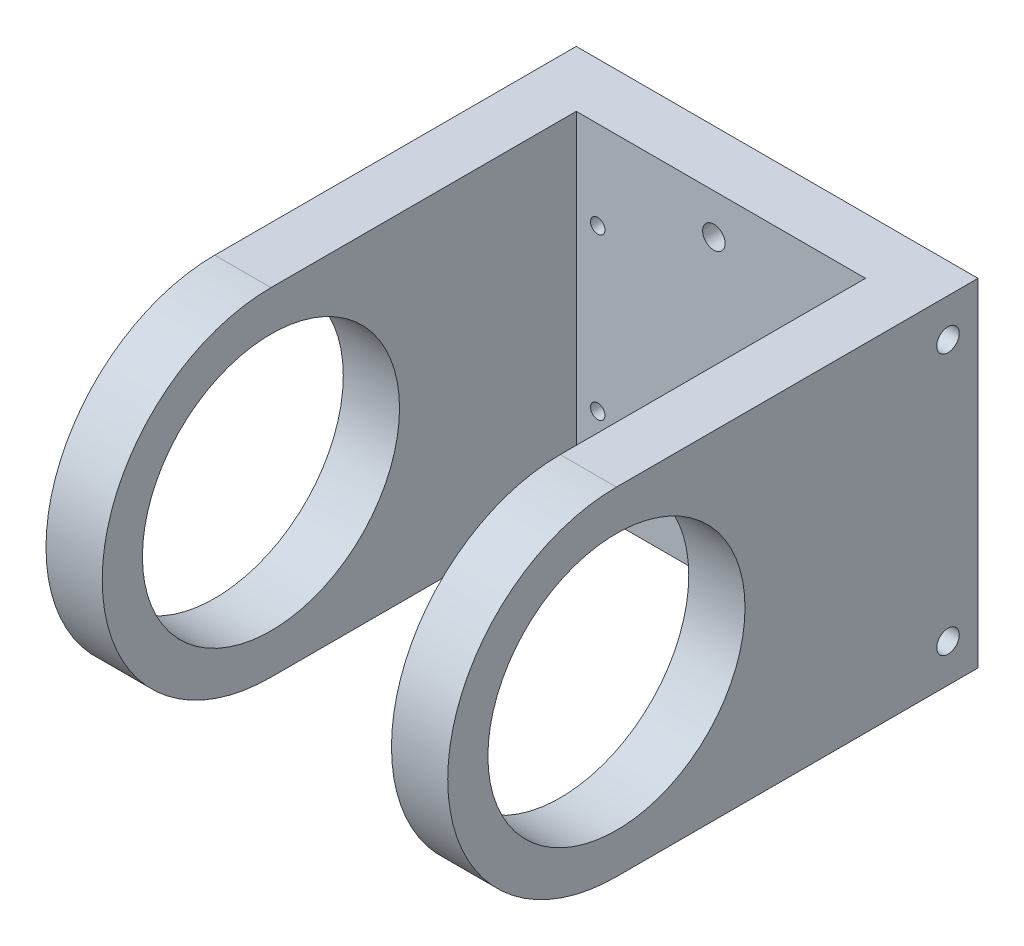
SolidWorks part; units mm, degrees
ref_plane "정면" through (0, 0, 0) normal (0, 0, 1) x (1, 0, 0)
ref_plane "윗면" through (0, 0, 0) normal (0, 1, 0) x (1, 0, 0)
ref_plane "우측면" through (0, 0, 0) normal (1, 0, 0) x (0, 0, -1)
ref_plane "평면1" through (-75, 0, 0) normal (-1, 0, 0) x (0, -1, 0)
sketch "스케치1" plane through (-75, 0, 0) normal (-1, 0, 0) x (0, -1, 0)
  line L0 (-21, 0) -> (-21, -45)
  line L1 (-21, -45) -> (21, -45)
  line L2 (21, -45) -> (21, 0)
  arc A0 (21, 0) -> (-21, 0) centre (0, 0) ccw
  dimension "D1" = 21
  dimension "D2" = 45
extrude "보스-돌출1" add sketch "스케치1" against normal blind 50
sketch "스케치2" plane through (0, 21, 0) normal (0, 1, 0) x (-1, 0, 0)
  line L0 (68, 64.1639) -> (32, 64.1639)
  line L1 (32, 64.1639) -> (32, -38)
  line L2 (32, -38) -> (68, -38)
  line L3 (68, -38) -> (68, 64.1639)
  line L4 (75, 0) -> (75, -45) construction
  line L5 (25, -45) -> (75, -45) construction
  line L6 (25, 0) -> (75, 0) construction
  circle A0 centre (50, 0) radius 21 construction
  dimension "D1" = 36
  dimension "D2" = 7
  dimension "D3" = 7
extrude "컷-돌출1" cut sketch "스케치2" against normal through all
hole_wizard "Ø1.8 (1.8) 지름 구멍1" positions "스케치4" profile "스케치3" hole size "Ø1.8" standard "Ansi Metric" end condition up to next
sketch "스케치4" plane through (0, 0, -45) normal (0, 0, -1) x (-1, 0, 0)
  point P12 (35.3332, 10)
  point P13 (65.3332, 10)
  point P14 (35.3332, -10)
  point P15 (65.3332, -10)
sketch "스케치3" plane through (-35.3332, 10, -45) normal (1, 0, 0) x (0, 1, 0)
  line L0 (0, 0) -> (0, 7)
  line L1 (0, 7) -> (0.9, 7)
  line L2 (0.9, 7) -> (0.9, 0)
  line L5 (0.9, 0) -> (0, 0)
  line L11 (0, -6.35) -> (0, 107.95) construction
  dimension "관통 구멍 지름" = 1.8
  dimension "관통 구멍 깊이" = 7
hole_wizard "M30 여유 구멍1" positions "스케치6" profile "스케치5" hole size "M30" standard "Ansi Metric" end condition up to next
sketch "스케치6" plane through (-25, 0, 0) normal (1, 0, 0) x (0, 0, -1)
  point P0 (0, 0)
sketch "스케치5" plane through (-25, 0, 0) normal (0, 1, 0) x (0, 0, -1)
  line L0 (0, 0) -> (0, 7)
  line L1 (0, 7) -> (16, 7)
  line L2 (16, 7) -> (16, 0)
  line L5 (16, 0) -> (0, 0)
  line L11 (0, -6.35) -> (0, 107.95) construction
  dimension "관통 구멍 지름" = 32
  dimension "관통 구멍 깊이" = 7
hole_wizard "M30 여유 구멍2" positions "스케치10" profile "스케치9" hole size "M30" standard "Ansi Metric" end condition up to next
sketch "스케치10" plane through (-75, 0, 0) normal (-1, 0, 0) x (0, 0, 1)
  point P0 (0, 0)
sketch "스케치9" plane through (-75, 0, 0) normal (0, 1, 0) x (0, 0, 1)
  line L0 (0, 0) -> (0, 7)
  line L1 (0, 7) -> (16, 7)
  line L2 (16, 7) -> (16, 0)
  line L5 (16, 0) -> (0, 0)
  line L11 (0, -6.35) -> (0, 107.95) construction
  dimension "관통 구멍 지름" = 32
  dimension "관통 구멍 깊이" = 7
sketch "스케치13" plane through (0, 0, -38) normal (0, 0, 1) x (1, 0, 0)
  line L0 (-32, -21) -> (-68, -21) construction
  line L1 (-32, 21) -> (-68, 21) construction
  circle A0 centre (-50.8768, -16) radius 1.4
  circle A1 centre (-50.8768, 16) radius 1.4
  dimension "D1" = 2.8
  dimension "D2" = 2.8
  dimension "D3" = 5
  dimension "D4" = 5
extrude "컷-돌출2" cut sketch "스케치13" against normal blind 10
sketch "스케치14" plane through (-25, 0, 0) normal (1, 0, 0) x (0, 0, -1)
  line L4 (45, -21) -> (0, -21) construction
  circle A0 centre (41.2671, 16.25) radius 1.4
  circle A1 centre (41.2671, -16.25) radius 1.4
  dimension "D1" = 2.8
  dimension "D2" = 2.8
  dimension "D4" = 4.75
  dimension "D3" = 32.5
extrude "컷-돌출3" cut sketch "스케치14" against normal blind 4
ref_plane "평면2" through (-50, 0, 0) normal (-1, 0, 0) x (0, 0, 1)
mirror "대칭 복사1" about plane through (-50, 0, 0) normal (-1, 0, 0) of "컷-돌출3"
